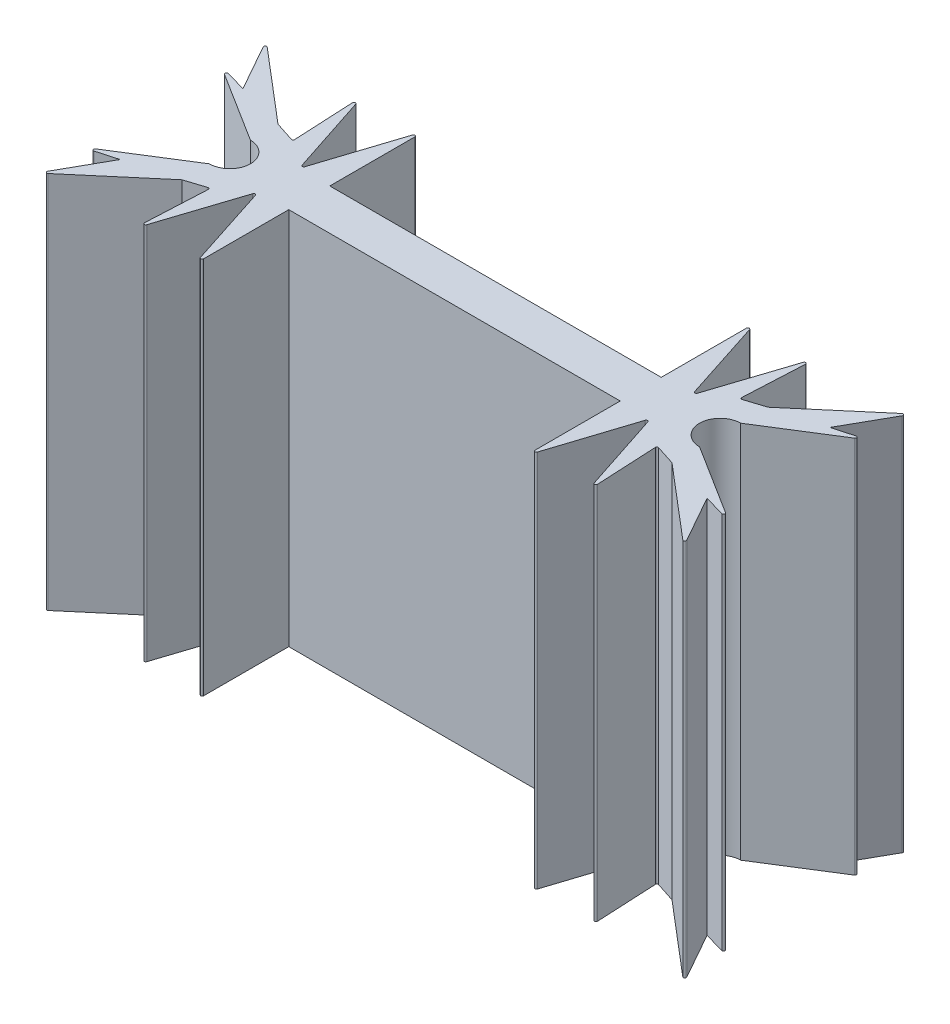
SolidWorks part; units mm, degrees
material "Медь"
ref_plane "Спереди" through (0, 0, 0) normal (0, 0, 1) x (1, 0, 0)
ref_plane "Сверху" through (0, 0, 0) normal (0, 1, 0) x (1, 0, 0)
ref_plane "Справа" through (0, 0, 0) normal (1, 0, 0) x (0, 0, -1)
sketch "Эскиз1" plane through (0, 0, 0) normal (0, 1, 0) x (1, 0, 0)
  line L0 (0, -7.3663) -> (0, -1.4307)
  line L17 (0.1951, 7.3971) -> (2.0315, 1.7231)
  line L18 (2.2217, 1.7228) -> (4.0437, 7.2908)
  line L19 (4.2386, 7.2548) -> (4.0271, 3.0093)
  line L20 (4.1577, 2.9092) -> (5.5364, 3.3554)
  line L21 (5.5364, 3.3554) -> (10.5735, 7.6374)
  line L22 (10.7254, 7.5122) -> (8.9077, 4.2831)
  line L23 (8.9077, 4.2831) -> (10.3379, 4.6831)
  line L24 (10.4181, 4.5021) -> (5.5364, 1.4307)
  line L25 (0, 0) -> (13.8384, 0) construction
  line L26 (10.4181, -4.5021) -> (5.5364, -1.4307)
  line L27 (8.9077, -4.2831) -> (10.3379, -4.6831)
  line L28 (10.7254, -7.5122) -> (8.9077, -4.2831)
  line L29 (5.5364, -3.3554) -> (10.5735, -7.6374)
  line L30 (4.1577, -2.9092) -> (5.5364, -3.3554)
  line L31 (4.2386, -7.2548) -> (4.0271, -3.0093)
  line L32 (2.2217, -1.7228) -> (4.0437, -7.2908)
  line L33 (0.1951, -7.3971) -> (2.0315, -1.7231)
  line L35 (0, 1.4307) -> (-23.12, 1.4307)
  line L38 (-23.12, -1.4307) -> (0, -1.4307)
  line L39 (0, 1.4307) -> (0, 7.3663)
  line L40 (-23.12, -7.3663) -> (-23.12, -1.4307)
  line L41 (-23.3151, -7.3971) -> (-25.1515, -1.7231)
  line L42 (-25.3417, -1.7228) -> (-27.1637, -7.2908)
  line L43 (-27.3586, -7.2548) -> (-27.1471, -3.0093)
  line L44 (-27.2777, -2.9092) -> (-28.6564, -3.3554)
  line L45 (-28.6564, -3.3554) -> (-33.6935, -7.6374)
  line L46 (-33.8454, -7.5122) -> (-32.0277, -4.2831)
  line L47 (-32.0277, -4.2831) -> (-33.4579, -4.6831)
  line L48 (-33.5381, -4.5021) -> (-28.6564, -1.4307)
  line L49 (-33.5381, 4.5021) -> (-28.6564, 1.4307)
  line L50 (-32.0277, 4.2831) -> (-33.4579, 4.6831)
  line L51 (-33.8454, 7.5122) -> (-32.0277, 4.2831)
  line L52 (-28.6564, 3.3554) -> (-33.6935, 7.6374)
  line L53 (-27.2777, 2.9092) -> (-28.6564, 3.3554)
  line L54 (-27.3586, 7.2548) -> (-27.1471, 3.0093)
  line L55 (-25.3417, 1.7228) -> (-27.1637, 7.2908)
  line L56 (-23.3151, 7.3971) -> (-25.1515, 1.7231)
  line L57 (-23.12, 1.4307) -> (-23.12, 7.3663)
  arc A0 (4.2386, 7.2548) -> (4.0437, 7.2908) centre (4.1388, 7.2597) ccw
  arc A1 (2.0315, 1.7231) -> (2.2217, 1.7228) centre (2.1267, 1.7539) ccw
  arc A2 (4.1577, 2.9092) -> (4.0271, 3.0093) centre (4.127, 3.0044) cw
  arc A3 (10.4181, 4.5021) -> (10.3379, 4.6831) centre (10.3649, 4.5867) ccw
  arc A4 (10.7254, 7.5122) -> (10.5735, 7.6374) centre (10.6383, 7.5612) ccw
  arc A5 (0, 7.3663) -> (0.1951, 7.3971) centre (0.1, 7.3663) cw
  arc A6 (0, -7.3663) -> (0.1951, -7.3971) centre (0.1, -7.3663) ccw
  arc A7 (10.7254, -7.5122) -> (10.5735, -7.6374) centre (10.6383, -7.5612) cw
  arc A8 (10.4181, -4.5021) -> (10.3379, -4.6831) centre (10.3649, -4.5867) cw
  arc A9 (4.1577, -2.9092) -> (4.0271, -3.0093) centre (4.127, -3.0044) ccw
  arc A10 (2.0315, -1.7231) -> (2.2217, -1.7228) centre (2.1267, -1.7539) cw
  arc A11 (4.2386, -7.2548) -> (4.0437, -7.2908) centre (4.1388, -7.2597) cw
  arc A12 (5.5364, 1.4307) -> (5.5364, -1.4307) centre (5.5364, 0) ccw
  arc A13 (-23.12, -7.3663) -> (-23.3151, -7.3971) centre (-23.22, -7.3663) cw
  arc A14 (-25.1515, -1.7231) -> (-25.3417, -1.7228) centre (-25.2467, -1.7539) ccw
  arc A15 (-27.3586, -7.2548) -> (-27.1637, -7.2908) centre (-27.2588, -7.2597) ccw
  arc A16 (-27.2777, -2.9092) -> (-27.1471, -3.0093) centre (-27.2469, -3.0044) cw
  arc A17 (-33.8454, -7.5122) -> (-33.6935, -7.6374) centre (-33.7583, -7.5612) ccw
  arc A18 (-33.5381, -4.5021) -> (-33.4579, -4.6831) centre (-33.4849, -4.5867) ccw
  arc A19 (-28.6564, 1.4307) -> (-28.6564, -1.4307) centre (-28.6564, 0) cw
  arc A20 (-33.5381, 4.5021) -> (-33.4579, 4.6831) centre (-33.4849, 4.5867) cw
  arc A21 (-33.8454, 7.5122) -> (-33.6935, 7.6374) centre (-33.7582, 7.5612) cw
  arc A22 (-27.2777, 2.9092) -> (-27.1471, 3.0093) centre (-27.2469, 3.0044) ccw
  arc A23 (-27.3586, 7.2548) -> (-27.1637, 7.2908) centre (-27.2588, 7.2597) cw
  arc A24 (-25.1515, 1.7231) -> (-25.3417, 1.7228) centre (-25.2467, 1.7539) cw
  arc A25 (-23.12, 7.3663) -> (-23.3151, 7.3971) centre (-23.22, 7.3663) ccw
  point P2 (0, 1.4307)
  point P4 (0, 0)
  point P5 (0, -4.1121)
  point P6 (11, -4.1121)
  point P7 (0, 1.4307)
  point P58 (0, -1.4307)
extrude "Бобышка-Вытянуть1" add sketch "Эскиз1" along normal blind 26.4 contours L35 L57 A25 L56 A24 L55 A23 L54 A22 L53 L52 A21 L51 L50 A20 L49 A19 L48 A18 L47 L46 A17 L45 L44 A16 L43 A15 L42 A14 L41 A13 L40 L38 L0 A6 L33 A10 L32 A11 L31 A9 L30 L29 A7 L28 L27 A8 L26 A12 L24 A3 L23 L22 A4 L21 L20 A2 L19 A0 L18 A1 L17 A5 L39
